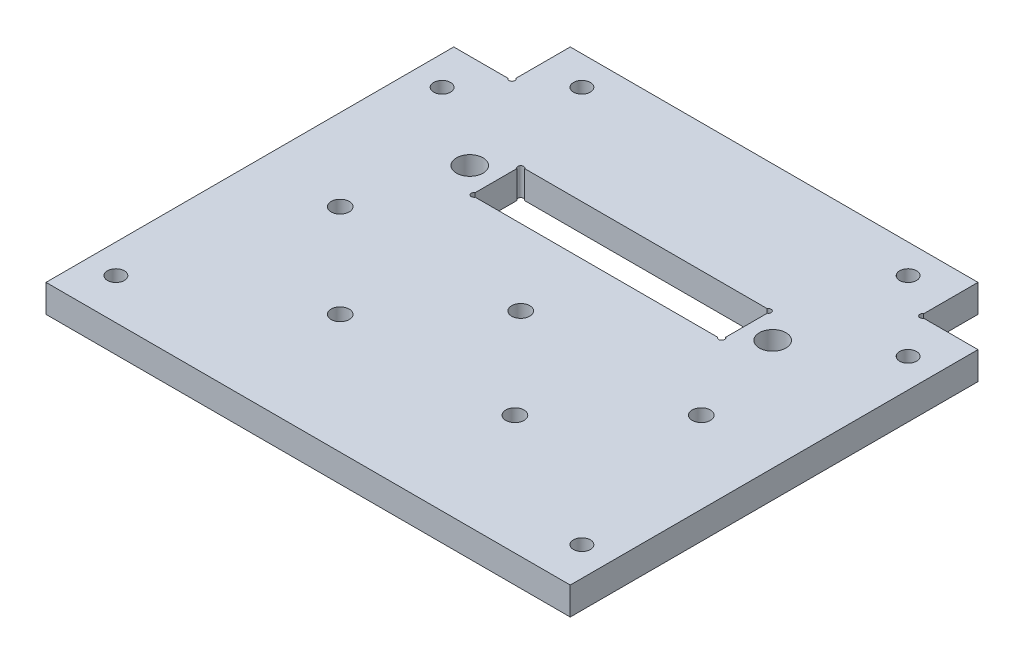
SolidWorks part; units mm, degrees
ref_plane "Front Plane" through (0, 0, 0) normal (0, 0, 1) x (1, 0, 0)
ref_plane "Top Plane" through (0, 0, 0) normal (0, 1, 0) x (1, 0, 0)
ref_plane "Right Plane" through (0, 0, 0) normal (1, 0, 0) x (0, 0, -1)
sketch "Sketch1" plane through (0, 0, 0) normal (0, 1, 0) x (1, 0, 0)
  line L0 (-35, 0) -> (-45, 0)
  line L1 (-35, 10) -> (35, 10)
  line L2 (-35, 10) -> (-35, 0)
  line L3 (0, 0) -> (0, 10) construction
  line L4 (35, 10) -> (35, 0)
  line L5 (45, 0) -> (35, 0)
  line L6 (45, 0) -> (45, -70)
  line L7 (45, -70) -> (-45, -70)
  line L8 (-45, 0) -> (-45, -70)
  dimension "D1" = 10
  dimension "D2" = 90
  dimension "D3" = 10
  dimension "D4" = 70
extrude "Base" add sketch "Sketch1" along normal blind 4.7625
sketch "Sketch2" plane through (0, 4.7625, 0) normal (0, 1, 0) x (1, 0, 0)
  line L0 (0, -33.5) -> (-31, -33.5) construction
  line L1 (0, -33.5) -> (31, -33.5) construction
  line L2 (-15, -49.5) -> (15, -49.5) construction
  line L3 (0, -41.5) -> (0, -49.5) construction
  circle A0 centre (-31, -33.5) radius 1.5625
  circle A1 centre (0, -33.5) radius 1.5625
  circle A2 centre (31, -33.5) radius 1.5625
  circle A3 centre (15, -49.5) radius 1.5625
  circle A4 centre (-15, -49.5) radius 1.5625
  point P10 (0, -41.5)
  dimension "D1" = 3.125
  dimension "D2" = 31
  dimension "D3" = 8
  dimension "D4" = 8
  dimension "D5" = 15
  dimension "D6" = 41.5
extrude "Cut-Extrude1" cut sketch "Sketch2" against normal through all
sketch "Sketch3" plane through (0, 4.7625, 0) normal (0, 1, 0) x (1, 0, 0)
  line L0 (0, -12) -> (0, 0) construction
  line L1 (-21.5, -12) -> (21.5, -12)
  line L2 (-21.5, -12) -> (-21.5, -20.5)
  line L3 (-21.5, -20.5) -> (21.5, -20.5)
  line L4 (21.5, -12) -> (21.5, -20.5)
  line L5 (-26, -16.25) -> (26, -16.25) construction
  line L6 (21.5, -20.5) -> (0, -16.25) construction
  line L7 (0, -16.25) -> (-21.5, -12) construction
  circle A0 centre (-26, -16.25) radius 2.286
  circle A1 centre (26, -16.25) radius 2.286
  dimension "D4" = 4.572
  dimension "D1" = 8.5
  dimension "D2" = 43
  dimension "D3" = 12
  dimension "D5" = 52
extrude "Cut-Extrude2" cut sketch "Sketch3" against normal through all
sketch "Sketch4" plane through (0, 4.7625, 0) normal (0, 1, 0) x (1, 0, 0)
  line L0 (-40, -63) -> (-40, 5) construction
  line L1 (-40, 5) -> (-3.8488, 5) construction
  line L2 (-45, -70) -> (45, -70) construction
  line L3 (-35, 0) -> (-45, 0) construction
  line L4 (-35, 10) -> (-35, 0) construction
  line L6 (0, 0) -> (0, -43.1233) construction
  circle A0 centre (-28, 5) radius 1.45
  circle A1 centre (-40, -7) radius 1.45
  circle A2 centre (-40, -63) radius 1.45
  circle A3 centre (40, -63) radius 1.45
  circle A4 centre (40, -7) radius 1.45
  circle A5 centre (28, 5) radius 1.45
  dimension "D1" = 2.9
  dimension "D2" = 7
  dimension "D3" = 7
  dimension "D4" = 7
  dimension "D5" = 5
  dimension "D6" = 40
extrude "Cut-Extrude3" cut sketch "Sketch4" against normal through all
sketch "Sketch5" plane through (0, 4.7625, 0) normal (0, 1, 0) x (1, 0, 0)
  line L0 (-21.25, -20.25) -> (-21.25, -20.5) construction
  line L1 (-21.5, -20.5) -> (21.5, -20.5) construction
  line L2 (-21.25, -20.25) -> (-21.5, -20.25) construction
  line L3 (-21.5, -12) -> (-21.5, -20.5) construction
  line L4 (-21.25, -12.25) -> (-21.5, -12.25) construction
  line L5 (-21.25, -12.25) -> (-21.25, -12) construction
  line L6 (21.5, -12) -> (-21.5, -12) construction
  line L7 (-35.25, 0.25) -> (-35.25, 0) construction
  line L8 (-35, 0) -> (-45, 0) construction
  line L9 (-35.25, 0.25) -> (-35, 0.25) construction
  line L10 (-35, 10) -> (-35, 0) construction
  line L11 (0, 0) -> (0, -17.9372) construction
  circle A0 centre (-35.25, 0.25) radius 0.5
  circle A1 centre (-21.25, -12.25) radius 0.5
  circle A2 centre (-21.25, -20.25) radius 0.5
  circle A3 centre (35.25, 0.25) radius 0.5
  circle A4 centre (21.25, -12.25) radius 0.5
  circle A5 centre (21.25, -20.25) radius 0.5
  dimension "D1" = 1
  dimension "D2" = 0.25
extrude "Cut-Extrude4" cut sketch "Sketch5" against normal through all
